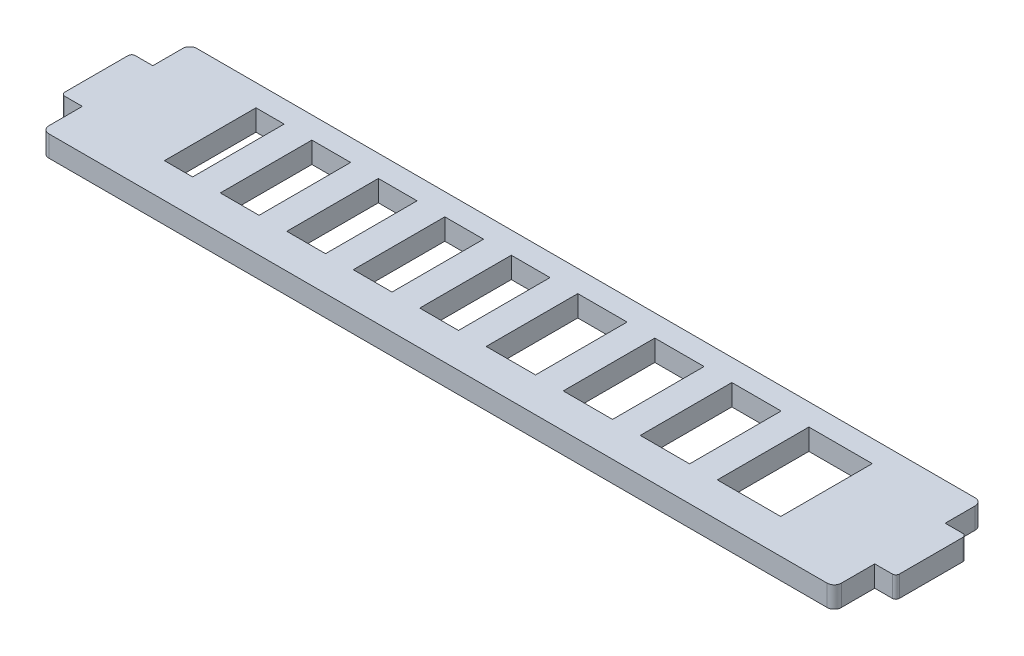
SolidWorks part; units mm, degrees
ref_plane "Спереди" through (0, 0, 0) normal (0, 0, 1) x (1, 0, 0)
ref_plane "Сверху" through (0, 0, 0) normal (0, 1, 0) x (1, 0, 0)
ref_plane "Справа" through (0, 0, 0) normal (1, 0, 0) x (0, 0, -1)
sketch "Эскиз1" plane through (0, 0, 0) normal (0, 1, 0) x (1, 0, 0)
  line L0 (0, -11.4) -> (0, 21.8864) construction
  line L1 (-56.25, -11.4) -> (56.25, -11.4)
  line L2 (56.25, -11.4) -> (56.25, -5.65)
  line L5 (56.25, -5.65) -> (59.25, -5.65)
  line L6 (59.25, -5.65) -> (59.25, 4.35)
  line L7 (59.25, 4.35) -> (56.25, 4.35)
  line L8 (56.25, 4.35) -> (56.25, 9.6)
  line L9 (56.25, 9.6) -> (-56.25, 9.6)
  line L10 (-56.25, 4.35) -> (-56.25, 9.6)
  line L11 (-59.25, 4.35) -> (-56.25, 4.35)
  line L12 (-59.25, -5.65) -> (-59.25, 4.35)
  line L13 (-56.25, -5.65) -> (-59.25, -5.65)
  line L16 (-56.25, -11.4) -> (-56.25, -5.65)
  line L22 (-30.3125, -6.5) -> (-26.375, -6.5) construction
  line L23 (-20.875, -6.5) -> (-16.9375, -6.5) construction
  line L63 (19.875, -6.5) -> (23.8125, -6.5) construction
  line L64 (30.8125, -6.5) -> (34.75, -6.5) construction
  line L69 (-39.75, -6.5) -> (-35.8125, -6.5) construction
  line L70 (-43.75, 6.5) -> (-39.75, 6.5)
  line L75 (-43.75, 6.5) -> (-43.75, -6.5)
  line L76 (-43.75, -6.5) -> (-39.75, -6.5)
  line L81 (-39.75, 6.5) -> (-39.75, -6.5)
  line L82 (-43.75, 6.5) -> (-39.75, -6.5) construction
  line L87 (-43.75, -6.5) -> (-39.75, 6.5) construction
  line L93 (34.75, 6.5) -> (43.75, 6.5)
  line L94 (34.75, 6.5) -> (34.75, -6.5)
  line L99 (34.75, -6.5) -> (43.75, -6.5)
  line L100 (43.75, 6.5) -> (43.75, -6.5)
  line L105 (34.75, 6.5) -> (43.75, -6.5) construction
  line L106 (34.75, -6.5) -> (43.75, 6.5) construction
  line L113 (-26.375, -6.5) -> (-20.875, -6.5)
  line L114 (-35.8125, 6.5) -> (-30.3125, 6.5)
  line L115 (-35.8125, 6.5) -> (-35.8125, -6.5)
  line L116 (-35.8125, -6.5) -> (-30.3125, -6.5)
  line L117 (-30.3125, 6.5) -> (-30.3125, -6.5)
  line L118 (-35.8125, 6.5) -> (-30.3125, -6.5) construction
  line L119 (-35.8125, -6.5) -> (-30.3125, 6.5) construction
  line L120 (-26.375, 6.5) -> (-20.875, 6.5)
  line L121 (-20.875, 6.5) -> (-20.875, -6.5)
  line L122 (-26.375, 6.5) -> (-26.375, -6.5)
  line L123 (-16.9375, -6.5) -> (-11.4375, -6.5)
  line L124 (-16.9375, 6.5) -> (-11.4375, 6.5)
  line L125 (-11.4375, 6.5) -> (-11.4375, -6.5)
  line L126 (-16.9375, 6.5) -> (-16.9375, -6.5)
  line L127 (-7.5, -6.5) -> (-2, -6.5)
  line L128 (-7.5, 6.5) -> (-2, 6.5)
  line L129 (-2, 6.5) -> (-2, -6.5)
  line L130 (-7.5, 6.5) -> (-7.5, -6.5)
  line L131 (12.875, 6.5) -> (19.875, 6.5)
  line L132 (1.9375, 6.5) -> (8.9375, 6.5)
  line L133 (1.9375, 6.5) -> (1.9375, -6.5)
  line L134 (1.9375, -6.5) -> (8.9375, -6.5)
  line L135 (8.9375, 6.5) -> (8.9375, -6.5)
  line L136 (1.9375, 6.5) -> (8.9375, -6.5) construction
  line L137 (1.9375, -6.5) -> (8.9375, 6.5) construction
  line L138 (12.875, 6.5) -> (12.875, -6.5)
  line L139 (19.875, 6.5) -> (19.875, -6.5)
  line L140 (12.875, -6.5) -> (19.875, -6.5)
  line L141 (23.8125, 6.5) -> (30.8125, 6.5)
  line L142 (23.8125, 6.5) -> (23.8125, -6.5)
  line L143 (30.8125, 6.5) -> (30.8125, -6.5)
  line L144 (23.8125, -6.5) -> (30.8125, -6.5)
  line L149 (-2, -6.5) -> (1.9375, -6.5) construction
  line L150 (-11.4375, -6.5) -> (-7.5, -6.5) construction
  line L151 (8.9375, -6.5) -> (12.875, -6.5) construction
  point P3 (39.25, 0)
  point P5 (-41.75, 0)
  point P14 (50, 0)
  point P22 (-33.0625, 0)
  point P25 (-50, 0)
  point P28 (43.75, 0)
  point P29 (30.5753, 6.5)
  point P75 (5.4375, 0)
  dimension "D5" = 13
  dimension "D11" = 5.5
  dimension "D1" = 3
  dimension "D2" = 10
  dimension "D3" = 6.25
  dimension "D4" = 21
  dimension "D6" = 5.25
  dimension "D7" = 100
  dimension "D8" = 9
  dimension "D9" = 9.6
  dimension "D10" = 4
  dimension "D12" = 7
  dimension "D13" = 6.25
  dimension "D14" = 6.25
extrude "Бобышка-Вытянуть1" add sketch "Эскиз1" along normal blind 3
fillet "Скругление1" radius 0.5 4 edges at (-59.25, 1.5, -4.35) (-59.25, 1.5, 5.65) (59.25, 1.5, -4.35) (59.25, 1.5, 5.65)
fillet "Скругление2" radius 1 4 edges at (56.25, 1.5, -9.6) (56.25, 1.5, 11.4) (-56.25, 1.5, -9.6) (-56.25, 1.5, 11.4)
